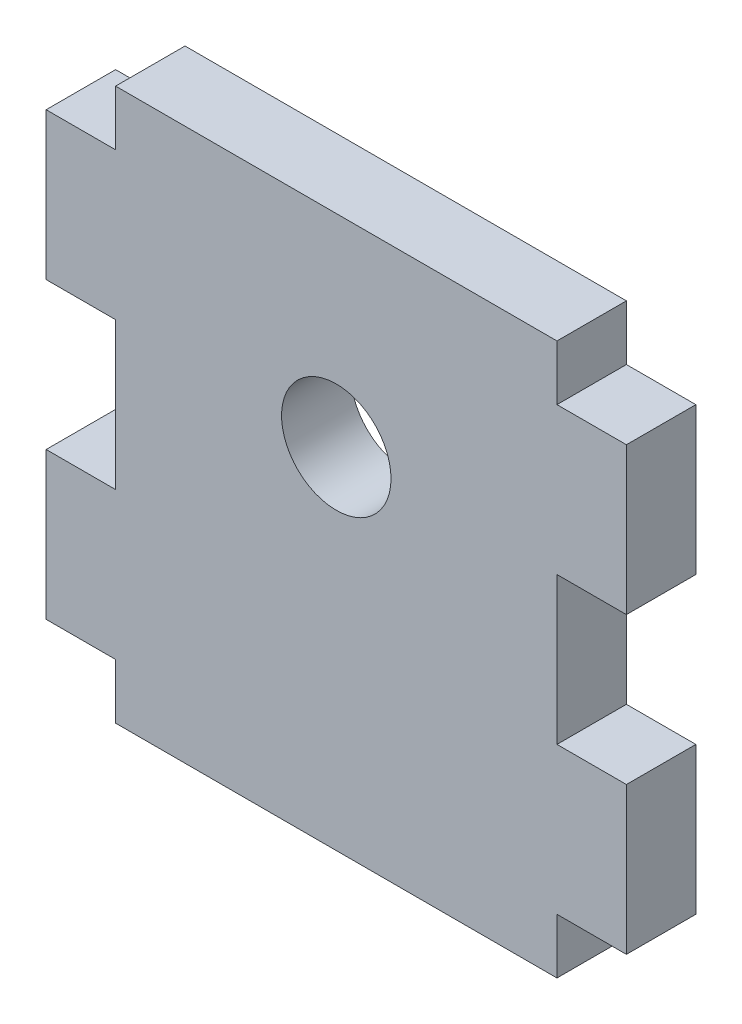
SolidWorks part; units mm, degrees
ref_plane "Front Plane" through (0, 0, 0) normal (0, 0, 1) x (1, 0, 0)
ref_plane "Top Plane" through (0, 0, 0) normal (0, 1, 0) x (1, 0, 0)
ref_plane "Right Plane" through (0, 0, 0) normal (1, 0, 0) x (0, 0, -1)
sketch "Sketch1" plane through (0, 0, 0) normal (0, 0, 1) x (1, 0, 0)
  line L0 (-38.1, 25.4) -> (0, 25.4) construction
  line L1 (0, 0) -> (-38.1, 0)
  line L2 (0, 0) -> (0, 6.35)
  line L3 (0, 50.8) -> (-38.1, 50.8)
  line L4 (-38.1, 0) -> (-38.1, 6.35)
  line L5 (-19.05, 0) -> (-19.05, 50.8) construction
  line L6 (-44.0944, 6.35) -> (-44.0944, 19.05)
  line L7 (-38.1, 44.45) -> (-44.0944, 44.45)
  line L8 (-38.1, 19.05) -> (-38.1, 31.75)
  line L9 (-38.1, 31.75) -> (-44.0944, 31.75)
  line L10 (-44.0944, 44.45) -> (-44.0944, 31.75)
  line L11 (-38.1, 19.05) -> (-44.0944, 19.05)
  line L12 (0, 19.05) -> (0, 31.75)
  line L13 (-38.1, 6.35) -> (-44.0944, 6.35)
  line L14 (0, 6.35) -> (5.9944, 6.35)
  line L15 (0, 44.45) -> (0, 50.8)
  line L16 (0, 19.05) -> (5.9944, 19.05)
  line L17 (5.9944, 44.45) -> (5.9944, 31.75)
  line L18 (0, 31.75) -> (5.9944, 31.75)
  line L20 (0, 44.45) -> (5.9944, 44.45)
  line L21 (5.9944, 6.35) -> (5.9944, 19.05)
  line L22 (-38.1, 44.45) -> (-38.1, 50.8)
  dimension "D1" = 38.1
  dimension "D2" = 50.8
  dimension "D3" = 5.9944
  dimension "D4" = 12.7
  dimension "D5" = 6.35
extrude "Boss-Extrude1" add sketch "Sketch1" along normal blind 5.9944
sketch "Sketch2" plane through (0, 0, 5.9944) normal (0, 0, 1) x (1, 0, 0)
  line L1 (-38.1, 0) -> (0, 0) construction
  circle A0 centre (-19.05, 31.75) radius 4.7244
  dimension "D1" = 9.4488
  dimension "D2" = 31.75
extrude "Cut-Extrude1" cut sketch "Sketch2" against normal through all
sketch "Sketch3" plane through (0, 0, 5.9944) normal (0, 0, 1) x (1, 0, 0)
  line L0 (0, 0) -> (0, 6.35) construction
  line L1 (-38.1, 0) -> (0, 0)
  line L2 (-38.1, 0) -> (-38.1, 1.5875)
  line L3 (-38.1, 1.5875) -> (0, 1.5875)
  line L4 (0, 0) -> (0, 1.5875)
  line L5 (-38.1, 50.8) -> (-38.1, 44.45) construction
  line L6 (0, 50.8) -> (-38.1, 50.8)
  line L7 (0, 50.8) -> (0, 49.2125)
  line L8 (0, 49.2125) -> (-38.1, 49.2125)
  line L9 (-38.1, 50.8) -> (-38.1, 49.2125)
  dimension "D1" = 1.5875
  dimension "D2" = 1.5875
extrude "Cut-Extrude2" cut sketch "Sketch3" against normal through all
